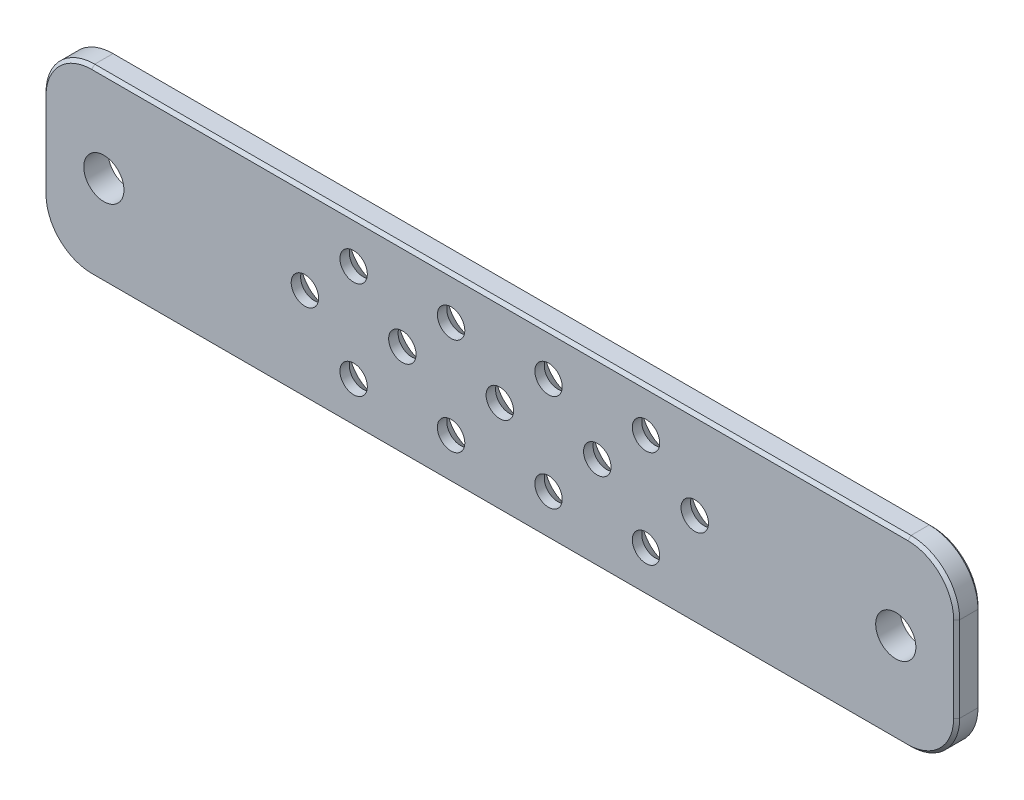
SolidWorks part; units mm, degrees
material "ABS"
ref_plane "Plan de face" through (0, 0, 0) normal (0, 0, 1) x (1, 0, 0)
ref_plane "Plan de dessus" through (0, 0, 0) normal (0, 1, 0) x (1, 0, 0)
ref_plane "Plan de droite" through (0, 0, 0) normal (1, 0, 0) x (0, 0, -1)
sketch "Esquisse1" plane through (0, 0, 0) normal (0, 0, 1) x (1, 0, 0)
  line L13 (75, -15) -> (-75, -15)
  line L14 (75, -15) -> (75, 15)
  line L15 (75, 15) -> (-75, 15)
  line L16 (-75, -15) -> (-75, 15)
  line L17 (75, -15) -> (-75, 15) construction
  line L18 (75, 15) -> (-75, -15) construction
  point P0 (0, 0)
extrude "Boss.-Extru.1" add sketch "Esquisse1" along normal blind 4
hole_wizard "Fraisage pour vis à tête fraisée M41" positions "Esquisse2" profile "Esquisse3" countersink size "M4" standard "Ansi Metric" end condition through all
sketch "Esquisse2" plane through (0, 0, 0) normal (0, 0, -1) x (-1, 0, 0)
  line L0 (75, -15) -> (-75, -15) construction
  line L2 (-75, -15) -> (-75, 15) construction
  point P0 (-8, 8)
  point P2 (-8, -8)
  point P4 (-16, 0.5844)
  point P6 (0, 0.5844)
  point P16 (8, 8)
  point P18 (8, -8)
  point P20 (16, 0.5844)
  point P26 (-24, 8)
  point P28 (-32, 0.5844)
  point P30 (-24, -8)
  point P32 (24, 8)
  point P34 (32, 0.5844)
  point P36 (24, -8)
  dimension "D1" = 16
  dimension "D2" = 8
  dimension "17mm" = 16
  dimension "D3" = 7
  dimension "D4" = 75
  dimension "D5" = 16
  dimension "D6" = 16
  dimension "D7" = 16
  dimension "D8" = 16
  dimension "D9" = 16
  dimension "D10" = 16
  dimension "D11" = 16
  dimension "D12" = 16
  dimension "D13" = 16
  dimension "D14" = 16
sketch "Esquisse3" plane through (8, 8, 0) normal (1, 0, 0) x (0, 1, 0)
  line L0 (0, 0) -> (0, 4)
  line L1 (0, 4) -> (2.25, 4)
  line L2 (2.25, 4) -> (2.25, 2.45)
  line L3 (2.25, 2.45) -> (4.7, 0)
  line L5 (4.7, 0) -> (0, 0)
  line L6 (-2.25, 2.45) -> (-4.7, 0) construction
  line L11 (0, -6.35) -> (0, 107.95) construction
  dimension "Diamètre du perçage jusqu'au prochain" = 4.5
  dimension "Profondeur du perçage jusqu'au prochain" = 4
  dimension "Diamètre du fraisage entrant" = 9.4
  dimension "Angle du fraisage entrant" = 90
hole_wizard "Dégagement M61" positions "Esquisse4" profile "Esquisse5" hole size "M6" standard "Ansi Metric" end condition through all
sketch "Esquisse4" plane through (0, 0, 0) normal (0, 0, -1) x (-1, 0, 0)
  line L0 (-75, 15) -> (75, 15) construction
  line L1 (-75, -15) -> (-75, 15) construction
  line L2 (75, 15) -> (75, -15) construction
  point P0 (-65, 0)
  point P2 (65, 0)
  dimension "D1" = 15
  dimension "D2" = 10
  dimension "D3" = 15
  dimension "D4" = 10
sketch "Esquisse5" plane through (65, 0, 0) normal (1, 0, 0) x (0, 1, 0)
  line L0 (0, 0) -> (0, 4)
  line L1 (0, 4) -> (3.3, 4)
  line L2 (3.3, 4) -> (3.3, 0)
  line L5 (3.3, 0) -> (0, 0)
  line L11 (0, -6.35) -> (0, 107.95) construction
  dimension "Diamètre du perçage jusqu'au prochain" = 6.6
  dimension "Profondeur du perçage jusqu'au prochain" = 4
fillet "Congé1" radius 8 4 edges at (-75, 15, 2) (75, 15, 2) (75, -15, 2) (-75, -15, 2)
chamfer "Chanfrein1" distance 0.5 angle 45 16 edges at (0, -15, 4) (72.6569, -12.6569, 4) (-72.6569, -12.6569, 4) (75, 0, 4) (-75, 0, 4) (72.6569, 12.6569, 4) (-72.6569, 12.6569, 4) (0, 15, 4) (0, -15, 0) (72.6569, -12.6569, 0) (-72.6569, -12.6569, 0) (75, 0, 0) (-75, 0, 0) (72.6569, 12.6569, 0) (-72.6569, 12.6569, 0) (0, 15, 0)
